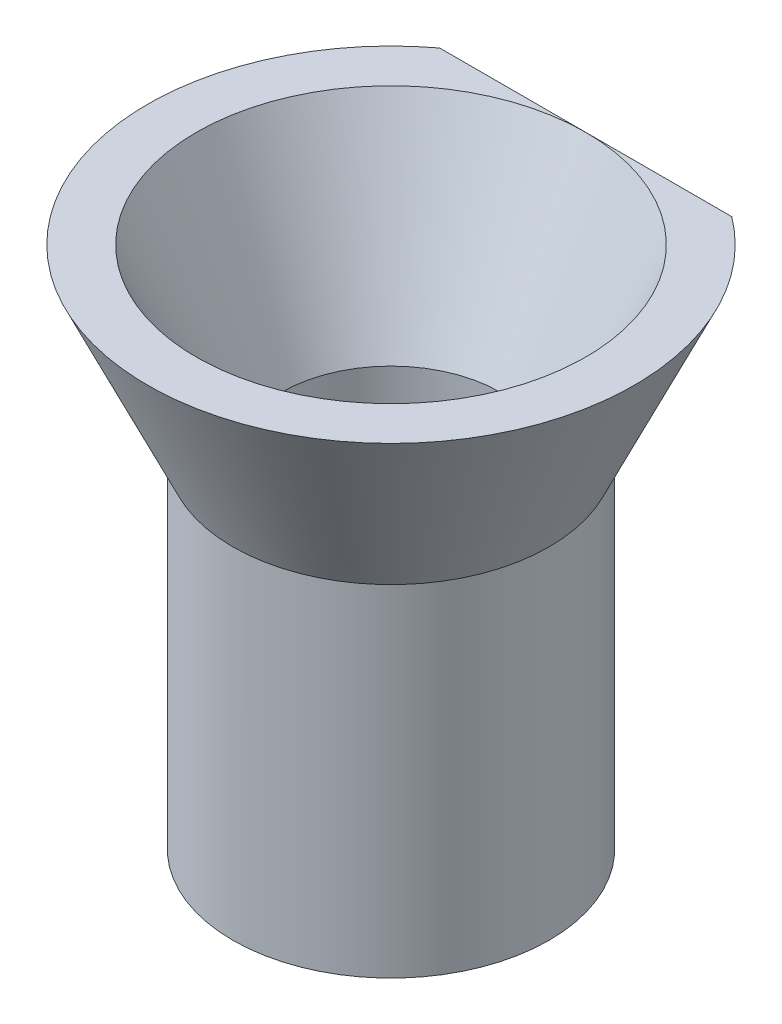
SolidWorks part; units mm, degrees
ref_plane "Alzado" through (0, 0, 0) normal (0, 0, 1) x (1, 0, 0)
ref_plane "Planta" through (0, 0, 0) normal (0, 1, 0) x (1, 0, 0)
ref_plane "Vista lateral" through (0, 0, 0) normal (1, 0, 0) x (0, 0, -1)
sketch "Croquis2" plane through (0, 0, 0) normal (0, 0, 1) x (1, 0, 0)
  line L0 (0, 0) -> (-4.5, 0) construction
  line L1 (-4.5, 0) -> (-8, 7.5)
  line L2 (-8, 7.5) -> (0, 7.5) construction
  line L3 (0, 7.5) -> (0, 0) construction
  line L4 (-8, 7.5) -> (-10, 7.5)
  line L5 (-10, 7.5) -> (-6.5, 0)
  line L6 (-6.5, 0) -> (-4.5, 0)
  dimension "D1" = 7.5
  dimension "D2" = 8
  dimension "D3" = 4.5
  dimension "D4" = 2
  dimension "D5" = 2
revolve "Revolución1" add sketch "Croquis2" angle 360 about L3
sketch "Croquis3" plane through (0, 0, 0) normal (0, -1, 0) x (1, 0, 0)
  circle A0 centre (0, 0) radius 4.5
  circle A1 centre (0, 0) radius 6.5
  dimension "D1" = 9
  dimension "D2" = 2
extrude "Saliente-Extruir1" add sketch "Croquis3" along normal blind 14
sketch "Croquis4" plane through (0, 7.5, 0) normal (0, 1, 0) x (1, 0, 0)
  line L0 (-7.1123, 8) -> (7.1123, 8)
  line L1 (7.1123, 8) -> (7.1123, 10.8305)
  line L2 (7.1123, 10.8305) -> (-7.1123, 10.8305)
  line L3 (-7.1123, 10.8305) -> (-7.1123, 8)
  point P3 (0, 8)
extrude "Cortar-Extruir1" cut sketch "Croquis4" against normal blind 7.5
